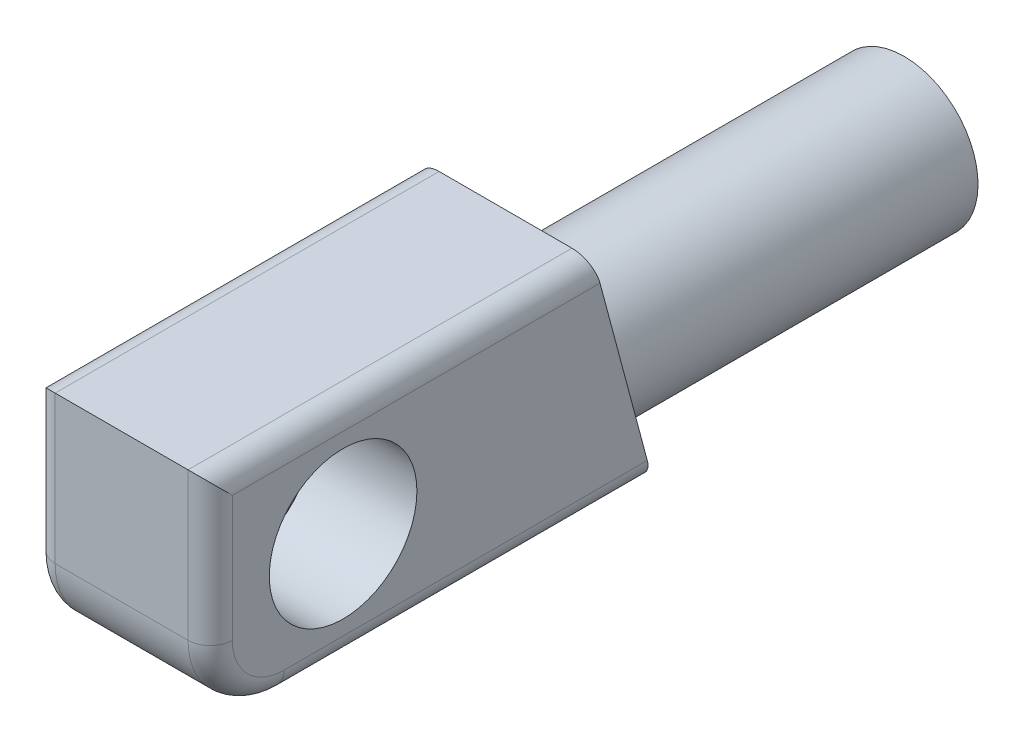
SolidWorks part; units mm, degrees
ref_plane "Front Plane" through (0, 0, 0) normal (0, 0, 1) x (1, 0, 0)
ref_plane "Top Plane" through (0, 0, 0) normal (0, 1, 0) x (1, 0, 0)
ref_plane "Right Plane" through (0, 0, 0) normal (1, 0, 0) x (0, 0, -1)
sketch "Sketch1" plane through (0, 0, 0) normal (1, 0, 0) x (0, 0, -1)
  line L0 (13, 7.5) -> (17, -7.5)
  line L1 (-13, -7.5) -> (13, -7.5) construction
  line L2 (-13, -7.5) -> (-13, 7.5) construction
  line L3 (-13, 7.5) -> (13, 7.5) construction
  line L4 (13, -7.5) -> (13, 7.5) construction
  line L5 (-13, -7.5) -> (13, 7.5) construction
  line L6 (-13, 7.5) -> (13, -7.5) construction
  line L7 (-13, -7.5) -> (17, -7.5)
  line L8 (-13, 7.5) -> (-13, -7.5)
  line L9 (-13, 7.5) -> (13, 7.5)
  point P0 (0, 0)
  dimension "D1" = 26
  dimension "D2" = 30
  dimension "D3" = 15
extrude "Boss-Extrude1" add sketch "Sketch1" along normal mid plane 12
sketch "Sketch2" plane through (0, 0, 0) normal (0, 0, 1) x (1, 0, 0)
  line L0 (0, 0) -> (0, -4.1844) construction
  line L1 (6, -7.5) -> (-6, -7.5) construction
  line L2 (-1, -6.5) -> (1, -6.5) construction
  line L3 (-1, -6.5) -> (-1, -7.5) construction
  line L4 (-1, -7.5) -> (1, -7.5)
  line L5 (1, -6.5) -> (1, -7.5) construction
  line L6 (-1, -6.5) -> (1, -7.5) construction
  line L7 (-1, -7.5) -> (1, -6.5) construction
  line L8 (-1, -7.5) -> (-1, -6.899)
  line L9 (1, -7.5) -> (1, -6.899)
  arc A0 (1, -6.899) -> (-1, -6.899) centre (0, -2) ccw
  circle A1 centre (0, -2) radius 4
  point P7 (0, -7)
  dimension "D1" = 10
  dimension "D2" = 8
  dimension "D3" = 2
  dimension "D4" = 2
extrude "Boss-Extrude2" add sketch "Sketch2" against normal blind 40 contours A0 A1
sketch "Sketch3" plane through (0, 0, 0) normal (1, 0, 0) x (0, 0, -1)
  line L0 (-4.9143, 0) -> (0, 0) construction
  circle A0 centre (-4, 0) radius 5
  dimension "D1" = 10
  dimension "D2" = 4
extrude "Cut-Extrude1" cut sketch "Sketch3" along normal through all from offset 1 offset against normal yes
fillet "Fillet1" radius 5 1 edges at (0, -7.5, 13)
fillet "Fillet2" radius 1.5 8 edges at (6, 2.5, 13) (6, -6.0355, 11.5355) (-6, -7.5, -4.5) (-6, -6.0355, 11.5355) (6, -7.5, -4.5) (6, 7.5, 0) (-6, 7.5, 0) (-6, 2.5, 13)
